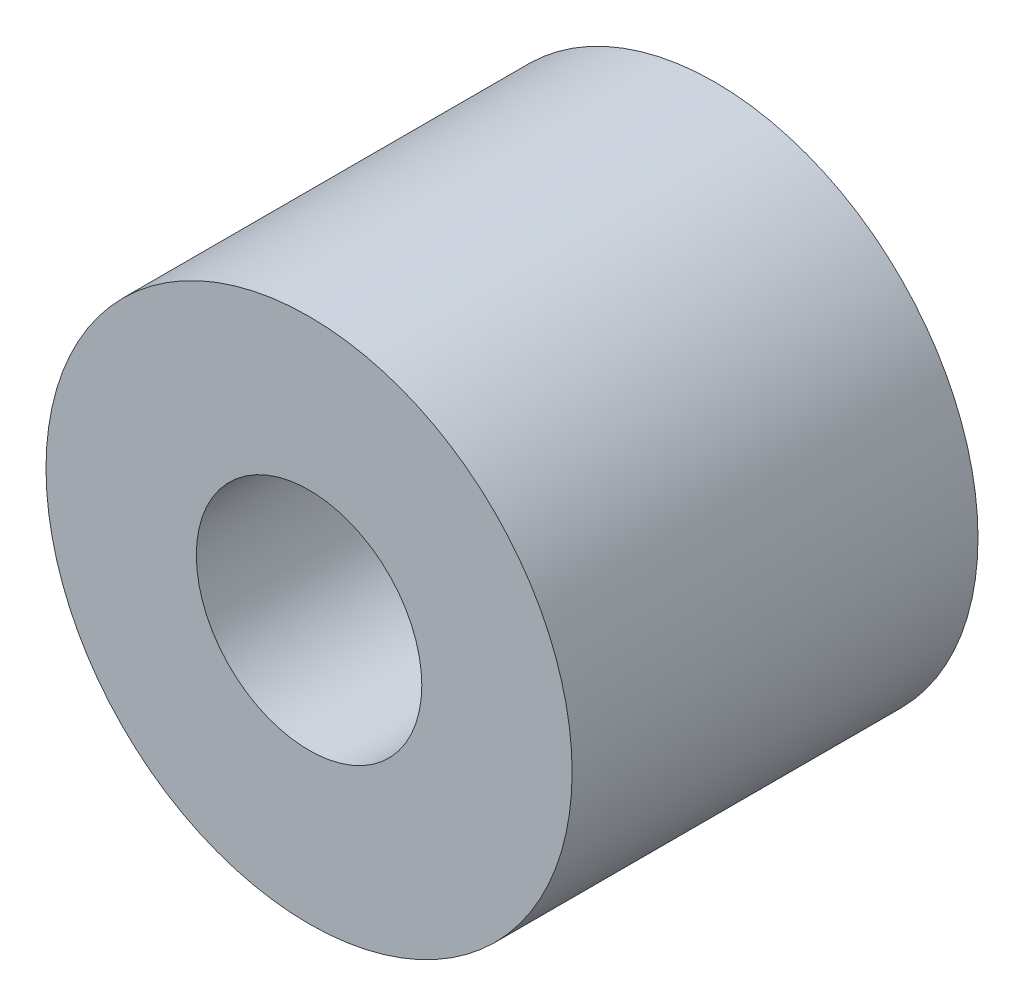
SolidWorks part; units mm, degrees
ref_plane "Front Plane" through (0, 0, 0) normal (0, 0, 1) x (1, 0, 0)
ref_plane "Top Plane" through (0, 0, 0) normal (0, 1, 0) x (1, 0, 0)
ref_plane "Right Plane" through (0, 0, 0) normal (1, 0, 0) x (0, 0, -1)
sketch "Sketch1" plane through (0, 0, 0) normal (0, 0, 1) x (1, 0, 0)
  circle A0 centre (0, 0) radius 1.5
  circle A2 centre (0, 0) radius 3.5
  dimension "D1" = 3
  dimension "D2" = 2
extrude "Boss-Extrude1" add sketch "Sketch1" along normal blind 5.4
